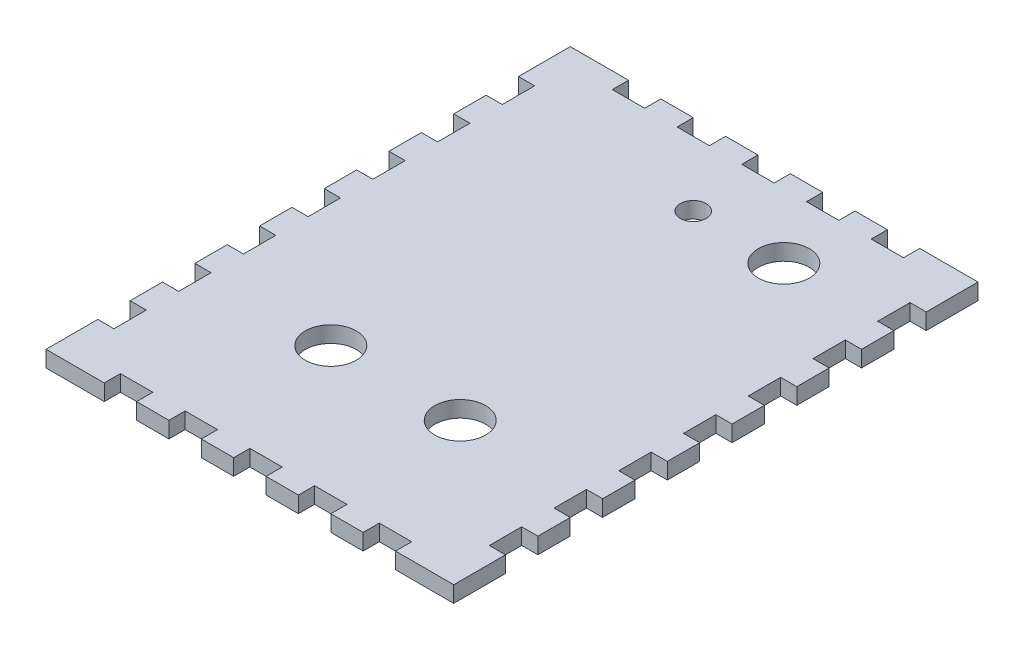
SolidWorks part; units mm, degrees
material "Acrylic (Medium-high impact)"
ref_plane "Front Plane" through (0, 0, 0) normal (0, 0, 1) x (1, 0, 0)
ref_plane "Top Plane" through (0, 0, 0) normal (0, 1, 0) x (1, 0, 0)
ref_plane "Right Plane" through (0, 0, 0) normal (1, 0, 0) x (0, 0, -1)
sketch "Sketch1" plane through (0, 0, 0) normal (0, 1, 0) x (1, 0, 0)
  line L1 (-40.005, 51.435) -> (40.005, 51.435)
  line L2 (-40.005, 51.435) -> (-40.005, -51.435)
  line L3 (-40.005, -51.435) -> (40.005, -51.435)
  line L4 (40.005, 51.435) -> (40.005, -51.435)
  line L5 (-40.005, 51.435) -> (40.005, -51.435) construction
  line L6 (-40.005, -51.435) -> (40.005, 51.435) construction
  point P0 (0, 0)
  dimension "D1" = 102.87
  dimension "D2" = 80.01
extrude "Boss-Extrude1" add sketch "Sketch1" along normal blind 3.175
sketch "Sketch2" plane through (0, 3.175, 0) normal (0, 1, 0) x (1, 0, 0)
  line L0 (-40.005, -41.275) -> (-36.83, -41.275)
  line L1 (-40.005, 51.435) -> (-40.005, -51.435) construction
  line L2 (-36.83, -41.275) -> (-36.83, -34.925)
  line L3 (-36.83, -34.925) -> (-40.005, -34.925)
  line L4 (-40.005, -51.435) -> (40.005, -51.435) construction
  line L5 (-40.005, -28.575) -> (-36.83, -28.575)
  line L6 (-40.005, 51.435) -> (-40.005, -51.435) construction
  line L7 (-36.83, -28.575) -> (-36.83, -22.225)
  line L8 (-36.83, -22.225) -> (-40.005, -22.225)
  line L9 (-40.005, -15.875) -> (-36.83, -15.875)
  line L10 (-36.83, -15.875) -> (-36.83, -9.525)
  line L11 (-36.83, -9.525) -> (-40.005, -9.525)
  line L12 (-40.005, -3.175) -> (-36.83, -3.175)
  line L13 (-36.83, -3.175) -> (-36.83, 3.175)
  line L14 (-36.83, 3.175) -> (-40.005, 3.175)
  line L15 (-40.005, 9.525) -> (-36.83, 9.525)
  line L16 (-36.83, 9.525) -> (-36.83, 15.875)
  line L17 (-36.83, 15.875) -> (-40.005, 15.875)
  line L18 (-40.005, 22.225) -> (-36.83, 22.225)
  line L19 (-36.83, 22.225) -> (-36.83, 28.575)
  line L20 (-36.83, 28.575) -> (-40.005, 28.575)
  line L21 (40.005, 51.435) -> (-40.005, 51.435) construction
  line L22 (-40.005, 51.435) -> (-40.005, -51.435) construction
  line L23 (-40.005, -34.925) -> (-40.005, -41.275)
  line L24 (-40.005, -22.225) -> (-40.005, -28.575)
  line L25 (-40.005, -9.525) -> (-40.005, -15.875)
  line L26 (-40.005, -3.175) -> (-40.005, 3.175)
  line L27 (-40.005, 15.875) -> (-40.005, 9.525)
  line L28 (-40.005, 28.575) -> (-40.005, 22.225)
  line L29 (0, 51.435) -> (0, -51.435) construction
  line L30 (40.005, 28.575) -> (40.005, 22.225)
  line L31 (40.005, 15.875) -> (40.005, 9.525)
  line L32 (40.005, -3.175) -> (40.005, 3.175)
  line L33 (40.005, -9.525) -> (40.005, -15.875)
  line L34 (40.005, -22.225) -> (40.005, -28.575)
  line L35 (40.005, -34.925) -> (40.005, -41.275)
  line L36 (36.83, 28.575) -> (40.005, 28.575)
  line L37 (36.83, 22.225) -> (36.83, 28.575)
  line L38 (40.005, 22.225) -> (36.83, 22.225)
  line L39 (36.83, 15.875) -> (40.005, 15.875)
  line L40 (36.83, 9.525) -> (36.83, 15.875)
  line L41 (40.005, 9.525) -> (36.83, 9.525)
  line L42 (36.83, 3.175) -> (40.005, 3.175)
  line L43 (36.83, -3.175) -> (36.83, 3.175)
  line L44 (40.005, -3.175) -> (36.83, -3.175)
  line L45 (36.83, -9.525) -> (40.005, -9.525)
  line L46 (36.83, -15.875) -> (36.83, -9.525)
  line L47 (40.005, -15.875) -> (36.83, -15.875)
  line L48 (36.83, -22.225) -> (40.005, -22.225)
  line L49 (36.83, -28.575) -> (36.83, -22.225)
  line L50 (40.005, -28.575) -> (36.83, -28.575)
  line L51 (36.83, -34.925) -> (40.005, -34.925)
  line L52 (36.83, -41.275) -> (36.83, -34.925)
  line L53 (40.005, -41.275) -> (36.83, -41.275)
  line L54 (-40.005, 34.925) -> (-36.83, 34.925)
  line L55 (-36.83, 34.925) -> (-36.83, 41.275)
  line L56 (-36.83, 41.275) -> (-40.005, 41.275)
  line L57 (-40.005, 41.275) -> (-40.005, 34.925)
  line L58 (40.005, 41.275) -> (40.005, 34.925)
  line L59 (36.83, 41.275) -> (40.005, 41.275)
  line L60 (36.83, 34.925) -> (36.83, 41.275)
  line L61 (40.005, 34.925) -> (36.83, 34.925)
  dimension "D1" = 3.175
  dimension "D2" = 6.35
  dimension "D3" = 10.16
  dimension "D4" = 6.35
  dimension "D5" = 6.35
  dimension "D6" = 6.35
  dimension "D7" = 6.35
  dimension "D8" = 6.35
  dimension "D9" = 10.16
  dimension "D10" = 6.35
extrude "Cut-Extrude1" cut sketch "Sketch2" against normal through all
sketch "Sketch3" plane through (0, 3.175, 0) normal (0, 1, 0) x (1, 0, 0)
  line L0 (28.575, 51.435) -> (28.575, 48.26)
  line L1 (40.005, 51.435) -> (-40.005, 51.435) construction
  line L2 (28.575, 48.26) -> (22.225, 48.26)
  line L3 (22.225, 48.26) -> (22.225, 51.435)
  line L4 (22.225, 51.435) -> (28.575, 51.435)
  line L5 (15.875, 51.435) -> (15.875, 48.26)
  line L6 (15.875, 48.26) -> (9.525, 48.26)
  line L7 (9.525, 48.26) -> (9.525, 51.435)
  line L8 (9.525, 51.435) -> (15.875, 51.435)
  line L9 (3.175, 51.435) -> (3.175, 48.26)
  line L10 (3.175, 48.26) -> (-3.175, 48.26)
  line L11 (-3.175, 48.26) -> (-3.175, 51.435)
  line L12 (-3.175, 51.435) -> (3.175, 51.435)
  line L13 (-9.525, 51.435) -> (-9.525, 48.26)
  line L14 (-9.525, 48.26) -> (-15.875, 48.26)
  line L15 (-15.875, 48.26) -> (-15.875, 51.435)
  line L16 (-15.875, 51.435) -> (-9.525, 51.435)
  line L17 (-40.005, 51.435) -> (-40.005, 41.275) construction
  line L18 (-36.83, 0) -> (36.83, 0) construction
  line L21 (-15.875, -51.435) -> (-9.525, -51.435)
  line L22 (-15.875, -48.26) -> (-15.875, -51.435)
  line L23 (-9.525, -48.26) -> (-15.875, -48.26)
  line L24 (-9.525, -51.435) -> (-9.525, -48.26)
  line L25 (40.005, 28.575) -> (40.005, 34.925) construction
  line L26 (-3.175, -51.435) -> (3.175, -51.435)
  line L27 (-3.175, -48.26) -> (-3.175, -51.435)
  line L28 (3.175, -48.26) -> (-3.175, -48.26)
  line L29 (3.175, -51.435) -> (3.175, -48.26)
  line L30 (9.525, -51.435) -> (15.875, -51.435)
  line L31 (9.525, -48.26) -> (9.525, -51.435)
  line L32 (15.875, -48.26) -> (9.525, -48.26)
  line L33 (15.875, -51.435) -> (15.875, -48.26)
  line L34 (22.225, -51.435) -> (28.575, -51.435)
  line L35 (22.225, -48.26) -> (22.225, -51.435)
  line L36 (28.575, -48.26) -> (22.225, -48.26)
  line L37 (28.575, -51.435) -> (28.575, -48.26)
  line L38 (36.83, 3.175) -> (36.83, -3.175) construction
  line L39 (-36.83, -3.175) -> (-36.83, 3.175) construction
  line L40 (-28.575, -51.435) -> (-22.225, -51.435)
  line L41 (-28.575, -48.26) -> (-28.575, -51.435)
  line L42 (-22.225, -48.26) -> (-28.575, -48.26)
  line L43 (-22.225, -51.435) -> (-22.225, -48.26)
  line L44 (-40.005, -51.435) -> (40.005, -51.435) construction
  line L45 (-22.225, 51.435) -> (-22.225, 48.26)
  line L46 (-22.225, 48.26) -> (-28.575, 48.26)
  line L47 (-28.575, 48.26) -> (-28.575, 51.435)
  line L48 (-28.575, 51.435) -> (-22.225, 51.435)
  dimension "D1" = 3.175
  dimension "D2" = 6.35
  dimension "D3" = 11.43
  dimension "D4" = 6.35
  dimension "D5" = 6.35
  dimension "D6" = 6.35
  dimension "D7" = 11.43
  dimension "D8" = 6.35
extrude "Cut-Extrude2" cut sketch "Sketch3" against normal through all
sketch "Sketch4" plane through (0, 3.175, 0) normal (0, 1, 0) x (1, 0, 0)
  line L1 (-27.305, 41.91) -> (27.305, 41.91) construction
  line L2 (-27.305, 41.91) -> (-27.305, -41.91) construction
  line L3 (-27.305, -41.91) -> (27.305, -41.91) construction
  line L4 (27.305, 41.91) -> (27.305, -41.91) construction
  line L5 (-27.305, 41.91) -> (27.305, -41.91) construction
  line L6 (-27.305, -41.91) -> (27.305, 41.91) construction
  circle A0 centre (0, 35.56) radius 2.54
  circle A1 centre (17.78, 35.56) radius 5
  circle A2 centre (12.7, -22.86) radius 5
  circle A3 centre (-12.7, -22.86) radius 5
  point P0 (0, 0)
  dimension "D12" = 5.08
  dimension "D13" = 6.35
  dimension "D14" = 27.305
  dimension "D3" = 10
  dimension "D4" = 9.525
  dimension "D6" = 10
  dimension "D7" = 10
  dimension "D1" = 54.61
  dimension "D2" = 83.82
  dimension "D5" = 6.35
  dimension "D8" = 12.7
  dimension "D9" = 12.7
  dimension "D10" = 19.05
  dimension "D11" = 19.05
extrude "Cut-Extrude3" cut sketch "Sketch4" against normal through all
